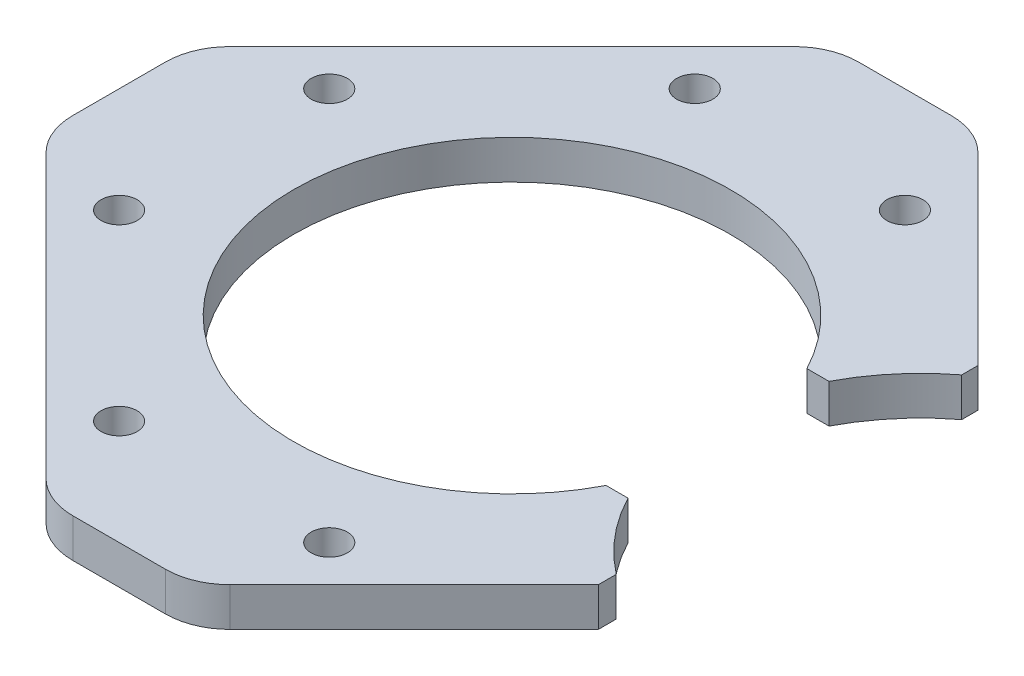
SolidWorks part; units mm, degrees
ref_plane "Front Plane" through (0, 0, 0) normal (0, 0, 1) x (1, 0, 0)
ref_plane "Top Plane" through (0, 0, 0) normal (0, 1, 0) x (1, 0, 0)
ref_plane "Right Plane" through (0, 0, 0) normal (1, 0, 0) x (0, 0, -1)
sketch "Sketch1" plane through (0, 0, 0) normal (0, 1, 0) x (1, 0, 0)
  line L0 (25.7425, 14.6901) -> (11.4915, 28.9411)
  line L1 (7.956, 30.4056) -> (0.7844, 30.4056)
  line L2 (-2.7512, 28.9411) -> (-24.571, 7.1213)
  line L3 (-26.0354, 3.5858) -> (-26.0354, -3.5858)
  line L4 (-24.571, -7.1213) -> (-2.7512, -28.9411)
  line L5 (0.7844, -30.4056) -> (7.956, -30.4056)
  line L6 (11.4915, -28.9411) -> (25.7425, -14.6901)
  line L7 (25.7425, 14.6901) -> (25.7425, 13.4311)
  line L8 (19.3311, 7.8601) -> (21.0391, 7.8601)
  line L9 (19.3924, -7.7423) -> (21.0904, -7.7423)
  line L10 (25.7425, -14.6901) -> (25.7425, -13.305)
  line L11 (-17.9037, 8.1317) -> (4.3702, 0) construction
  line L12 (-17.9037, -8.1317) -> (4.3702, 0) construction
  line L13 (-3.7616, 22.2739) -> (4.3702, 0) construction
  circle A0 centre (12.5019, -22.2739) radius 1.4
  circle A1 centre (-3.7616, -22.2739) radius 1.4
  circle A2 centre (-17.9037, -8.1317) radius 1.4
  circle A3 centre (-17.9037, 8.1317) radius 1.4
  circle A4 centre (-3.7616, 22.2739) radius 1.4
  circle A5 centre (12.5019, 22.2739) radius 1.4
  arc A7 (11.4915, 28.9411) -> (7.956, 30.4056) centre (7.956, 25.4056) ccw
  arc A8 (0.7844, 30.4056) -> (-2.7512, 28.9411) centre (0.7844, 25.4056) ccw
  arc A9 (-24.571, 7.1213) -> (-26.0354, 3.5858) centre (-21.0354, 3.5858) ccw
  arc A10 (-26.0354, -3.5858) -> (-24.571, -7.1213) centre (-21.0354, -3.5858) ccw
  arc A11 (-2.7512, -28.9411) -> (0.7844, -30.4056) centre (0.7844, -25.4056) ccw
  arc A12 (7.956, -30.4056) -> (11.4915, -28.9411) centre (7.956, -25.4056) ccw
  arc A14 (21.0904, -7.7423) -> (25.7425, -13.305) centre (36, 0) ccw
  arc A16 (19.3311, 7.8601) -> (19.3924, -7.7423) centre (4.3702, 0) ccw
  arc A18 (25.7425, 13.4311) -> (21.0391, 7.8601) centre (36, 0) ccw
  dimension "D1" = 51
  dimension "D2" = 16.9
  dimension "D3" = 16.9
  dimension "D4" = 16.8
  dimension "D5" = 2.8
  dimension "D6" = 36
extrude "Boss-Extrude1" add sketch "Sketch1" along normal blind 3
